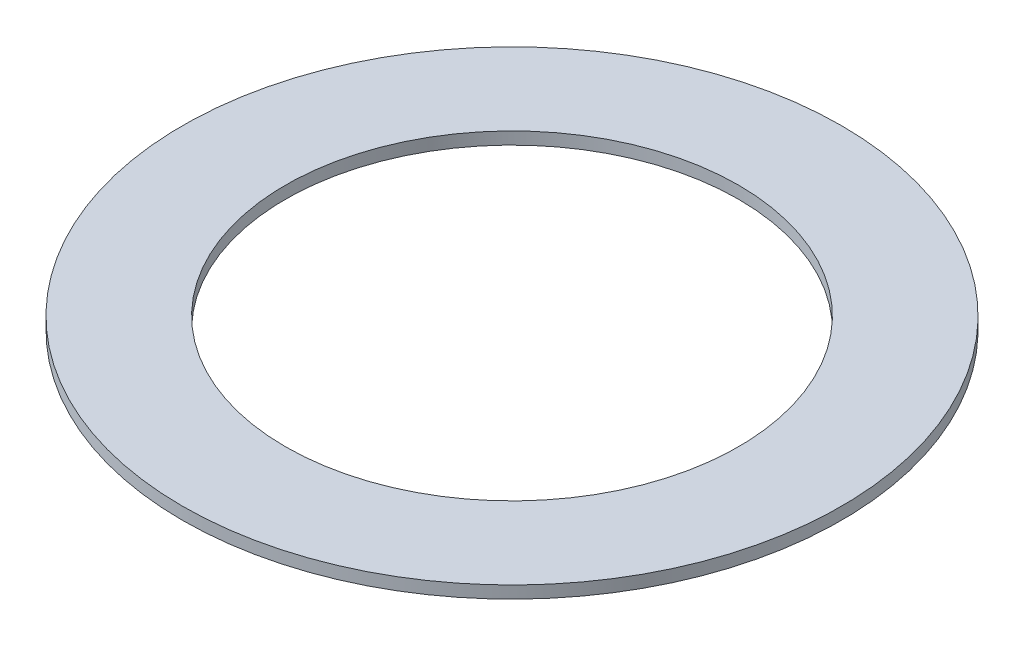
SolidWorks part; units mm, degrees
material "6063-T6"
ref_plane "Front Plane" through (0, 0, 0) normal (0, 0, 1) x (1, 0, 0)
ref_plane "Top Plane" through (0, 0, 0) normal (0, 1, 0) x (1, 0, 0)
ref_plane "Right Plane" through (0, 0, 0) normal (1, 0, 0) x (0, 0, -1)
sketch "Sketch1" plane through (0, 0, 0) normal (0, 1, 0) x (1, 0, 0)
  circle A0 centre (0, 0) radius 6.5659
  circle A1 centre (0, 0) radius 9.5504
  dimension "D1" = 13.1318
  dimension "D2" = 19.1008
extrude "Boss-Extrude1" add sketch "Sketch1" along normal blind 0.3556
